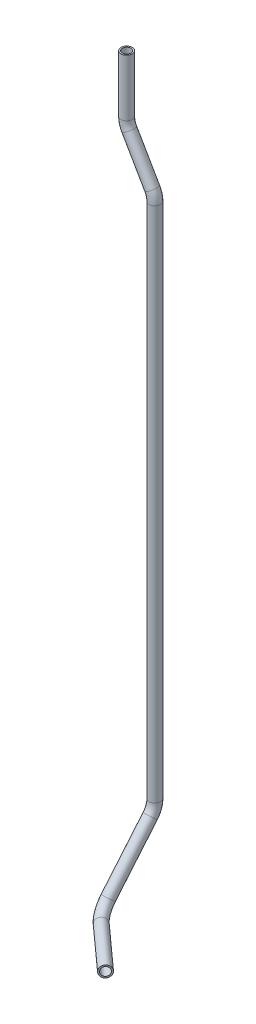
SolidWorks part; units mm, degrees
ref_plane "Plane1" through (0, 0, 0) normal (0, 0, 1) x (1, 0, 0)
ref_plane "Plane2" through (0, 0, 0) normal (0, 1, 0) x (1, 0, 0)
ref_plane "Plane3" through (0, 0, 0) normal (1, 0, 0) x (0, 0, -1)
sketch3d "3DSketch1"
  line L0 (0, 0, 0) -> (0, -60.3731, 0)
  line L1 (2.8135, -70.8731, 0) -> (27.1865, -113.0885, 0)
  line L2 (30, -123.5885, 0) -> (30, -672.7349, 0)
  line L3 (30, -686.2335, 4.9131) -> (30, -739.3449, 49.4789)
  line L4 (39.8515, -749.5, 66.8704) -> (86.0859, -749.5, 108.5)
  line L5 (0, 0, 0) -> (0, -749.5, 0) construction
  line L6 (30, -749.5, 0) -> (0, -749.5, 0) construction
  line L7 (30, -749.5, 0) -> (30, -749.5, 108.5) construction
  line L8 (30, -672.7349, 0) -> (30, -749.5, 0) construction
  line L9 (30, -749.5, 108.5) -> (86.0859, -749.5, 108.5) construction
  arc A0 (0, -60.3731, 0) -> (2.8135, -70.8731, 0) centre (21, -60.3731, 0) ccw
  arc A1 (27.1865, -113.0885, 0) -> (30, -123.5885, 0) centre (9, -123.5885, 0) ccw
  arc A2 (30, -672.7349, 0) -> (30, -686.2335, 4.9131) centre (30, -672.7349, 21) ccw
  arc A3 (30, -739.3449, 49.4789) -> (39.8515, -749.5, 66.8704) centre (47.2867, -731.6806, 58.6128) ccw
  point P6 (30, -680.3783, 0)
  point P10 (0, -66, 0)
  point P11 (21, -60.3731, 21)
  point P14 (30, -117.9615, 0)
  point P15 (9, -123.5885, -21)
  point P18 (30, -741, 0)
  point P20 (9, -672.7349, 21)
  point P23 (30, -749.5, 58)
  point P24 (35.3632, -720.5689, 71.8552)
  dimension "D7" = 21
  dimension "D8" = 21
  dimension "D9" = 21
  dimension "D10" = 21
  dimension "D1" = 66
  dimension "D2" = 150
  dimension "D3" = 30
  dimension "D4" = 58
  dimension "D13" = 50
  dimension "D5" = 108.5
  dimension "D11" = 50.5
  dimension "D6" = 749.5
  dimension "D12" = 48
sketch "Sketch2" plane through (0, 0, 0) normal (0, 1, 0) x (1, 0, 0)
  circle A0 centre (0, 0) radius 6
  circle A1 centre (0, 0) radius 4.5
  dimension "D1" = 12
  dimension "D2" = 1.5
sweep "Sweep1" add profiles "Sketch2" path "3DSketch1"
